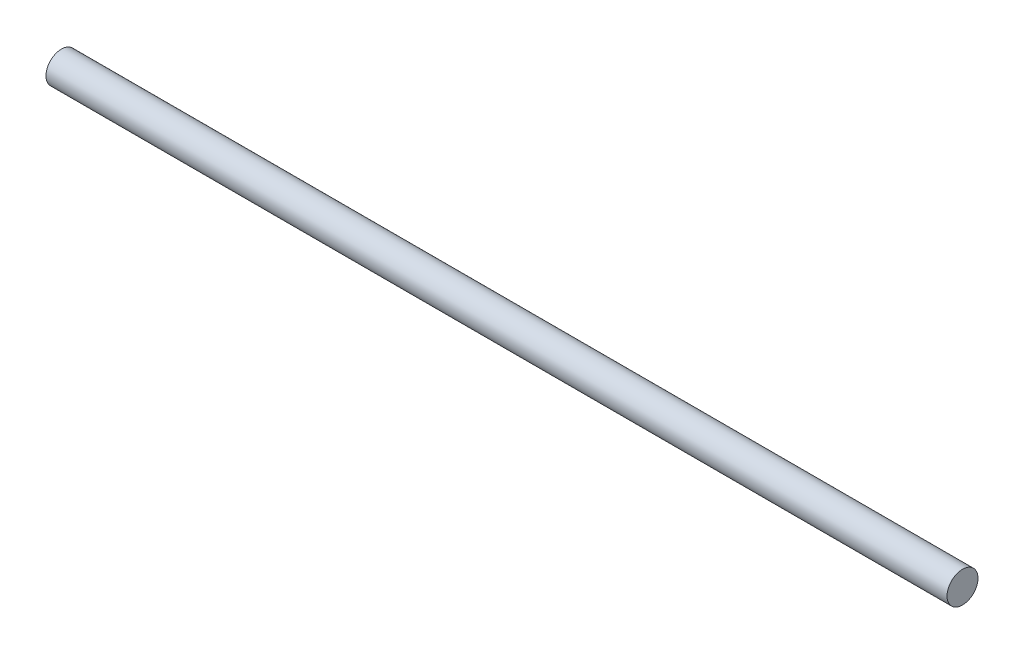
SolidWorks part; units mm, degrees
ref_plane "Front Plane" through (0, 0, 0) normal (0, 0, 1) x (1, 0, 0)
ref_plane "Top Plane" through (0, 0, 0) normal (0, 1, 0) x (1, 0, 0)
ref_plane "Right Plane" through (0, 0, 0) normal (1, 0, 0) x (0, 0, -1)
sketch "Sketch1" plane through (0, 0, 0) normal (1, 0, 0) x (0, 0, -1)
  circle A0 centre (0, 0) radius 15
extrude "Boss-Extrude1" add sketch "Sketch1" along normal blind 873
